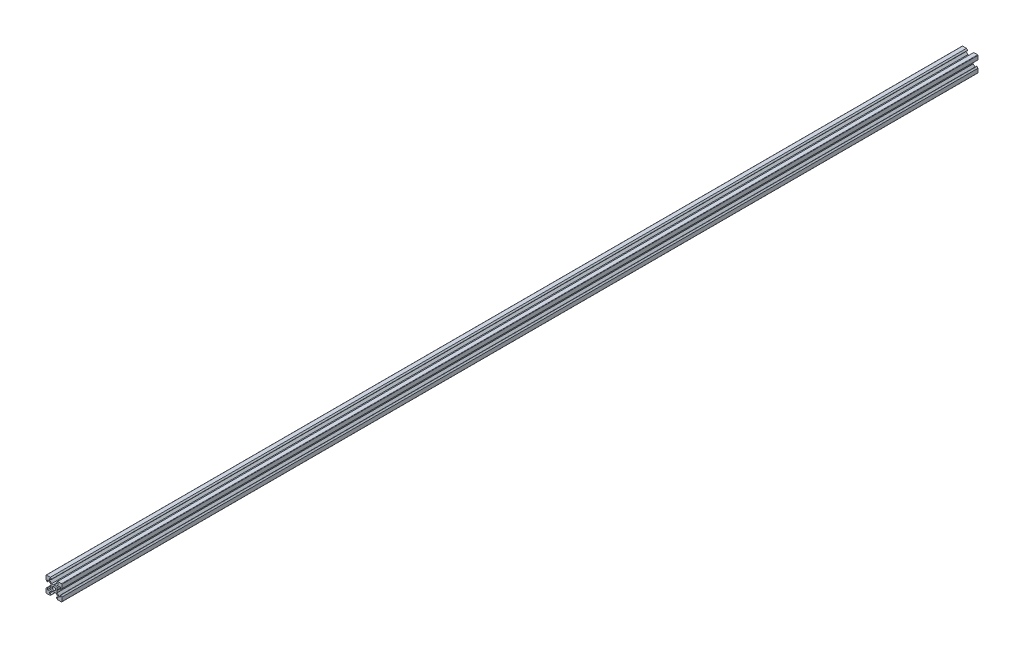
SolidWorks part; units mm, degrees
material "6061-T6 (SS)"
ref_plane "Front Plane" through (0, 0, 0) normal (0, 0, 1) x (1, 0, 0)
ref_plane "Top Plane" through (0, 0, 0) normal (0, 1, 0) x (1, 0, 0)
ref_plane "Right Plane" through (0, 0, 0) normal (1, 0, 0) x (0, 0, -1)
sketch "Sketch1" plane through (0, 0, 0) normal (0, 0, 1) x (1, 0, 0)
  line L1 (9.5, -10) -> (-9.5, -10)
  line L2 (10, -9.5) -> (10, 9.5)
  line L3 (9.5, 10) -> (-9.5, 10)
  line L4 (-10, -9.5) -> (-10, 9.5)
  line L5 (10, -10) -> (-10, 10) construction
  line L6 (10, 10) -> (-10, -10) construction
  circle A0 centre (0, 0) radius 2.1
  arc A1 (-9.5, 10) -> (-10, 9.5) centre (-9.5, 9.5) ccw
  arc A2 (10, 9.5) -> (9.5, 10) centre (9.5, 9.5) ccw
  arc A3 (9.5, -10) -> (10, -9.5) centre (9.5, -9.5) ccw
  arc A4 (-9.5, -10) -> (-10, -9.5) centre (-9.5, -9.5) cw
  point P0 (0, 0)
  line B0 (0, 0) -> (0, 10) construction
  line B1 (0, 3.69) -> (-0.21, 3.9)
  line B2 (-0.21, 3.9) -> (-2.8393, 3.9)
  line B3 (-2.8393, 3.9) -> (-5.5, 6.5607)
  line B4 (-5.5, 6.5607) -> (-5.5, 8.2)
  line B5 (-5.5, 8.2) -> (-3.125, 8.2)
  line B6 (-3.125, 8.2) -> (-3.125, 8.545)
  line B7 (-3.125, 8.545) -> (-4.58, 10)
  line B8 (-4.58, 10) -> (4.58, 10)
  line B9 (0, 0) -> (-5.9132, 5.9132) construction
  line B10 (3.125, 8.545) -> (4.58, 10)
  line B11 (3.125, 8.2) -> (3.125, 8.545)
  line B12 (5.5, 8.2) -> (3.125, 8.2)
  line B13 (5.5, 6.5607) -> (5.5, 8.2)
  line B14 (2.8393, 3.9) -> (5.5, 6.5607)
  line B15 (0.21, 3.9) -> (2.8393, 3.9)
  line B16 (0, 3.69) -> (0.21, 3.9)
  line B17 (0, 0) -> (-10, 0) construction
  line B18 (-3.69, 0) -> (-3.9, -0.21)
  line B19 (-3.9, -0.21) -> (-3.9, -2.8393)
  line B20 (-3.9, -2.8393) -> (-6.5607, -5.5)
  line B21 (-6.5607, -5.5) -> (-8.2, -5.5)
  line B22 (-8.2, -5.5) -> (-8.2, -3.125)
  line B23 (-8.2, -3.125) -> (-8.545, -3.125)
  line B24 (-8.545, -3.125) -> (-10, -4.58)
  line B25 (-10, -4.58) -> (-10, 4.58)
  line B26 (0, 0) -> (-5.9132, -5.9132) construction
  line B27 (-8.545, 3.125) -> (-10, 4.58)
  line B28 (-8.2, 3.125) -> (-8.545, 3.125)
  line B29 (-8.2, 5.5) -> (-8.2, 3.125)
  line B30 (-6.5607, 5.5) -> (-8.2, 5.5)
  line B31 (-3.9, 2.8393) -> (-6.5607, 5.5)
  line B32 (-3.9, 0.21) -> (-3.9, 2.8393)
  line B33 (-3.69, 0) -> (-3.9, 0.21)
  line B34 (0, 0) -> (0, -10) construction
  line B35 (0, -3.69) -> (0.21, -3.9)
  line B36 (0.21, -3.9) -> (2.8393, -3.9)
  line B37 (2.8393, -3.9) -> (5.5, -6.5607)
  line B38 (5.5, -6.5607) -> (5.5, -8.2)
  line B39 (5.5, -8.2) -> (3.125, -8.2)
  line B40 (3.125, -8.2) -> (3.125, -8.545)
  line B41 (3.125, -8.545) -> (4.58, -10)
  line B42 (4.58, -10) -> (-4.58, -10)
  line B43 (0, 0) -> (5.9132, -5.9132) construction
  line B44 (-3.125, -8.545) -> (-4.58, -10)
  line B45 (-3.125, -8.2) -> (-3.125, -8.545)
  line B46 (-5.5, -8.2) -> (-3.125, -8.2)
  line B47 (-5.5, -6.5607) -> (-5.5, -8.2)
  line B48 (-2.8393, -3.9) -> (-5.5, -6.5607)
  line B49 (-0.21, -3.9) -> (-2.8393, -3.9)
  line B50 (0, -3.69) -> (-0.21, -3.9)
  line B51 (0, 0) -> (10, 0) construction
  line B52 (3.69, 0) -> (3.9, 0.21)
  line B53 (3.9, 0.21) -> (3.9, 2.8393)
  line B54 (3.9, 2.8393) -> (6.5607, 5.5)
  line B55 (6.5607, 5.5) -> (8.2, 5.5)
  line B56 (8.2, 5.5) -> (8.2, 3.125)
  line B57 (8.2, 3.125) -> (8.545, 3.125)
  line B58 (8.545, 3.125) -> (10, 4.58)
  line B59 (10, 4.58) -> (10, -4.58)
  line B60 (0, 0) -> (5.9132, 5.9132) construction
  line B61 (8.545, -3.125) -> (10, -4.58)
  line B62 (8.2, -3.125) -> (8.545, -3.125)
  line B63 (8.2, -5.5) -> (8.2, -3.125)
  line B64 (6.5607, -5.5) -> (8.2, -5.5)
  line B65 (3.9, -2.8393) -> (6.5607, -5.5)
  line B66 (3.9, -0.21) -> (3.9, -2.8393)
  line B67 (3.69, 0) -> (3.9, -0.21)
  dimension "D1" = 4.2
  dimension "D3" = 0.5
  dimension "D2" = 20
sketch_block_instance "V Slot 1-4"
sketch_block "V Slot 1" parameters "D1"=10, "D2"=11, "D3"=4.3, "D4"=1.8, "D5"=0.21, "D6"=45, "D7"=9.16, "D8"=1.5, "D9"=6.25
sketch_block_instance "V Slot 1-5"
sketch_block_instance "V Slot 1-6"
sketch_block_instance "V Slot 1-7"
extrude "Boss-Extrude1" add sketch "Sketch1" along normal blind 1160 contours B67 B52 B53 B54 B55 B56 B57 B58 L2 A2 L3 B10 B11 B12 B13 B14 B15 B16 B1 B2 B3 B4 B5 B6 B7 A1 L4 B27 B28 B29 B30 B31 B32 B33 B18 B19 B20 B21 B22 B23 B24 A4 L1 B44 B45 B46 B47 B48 B49
